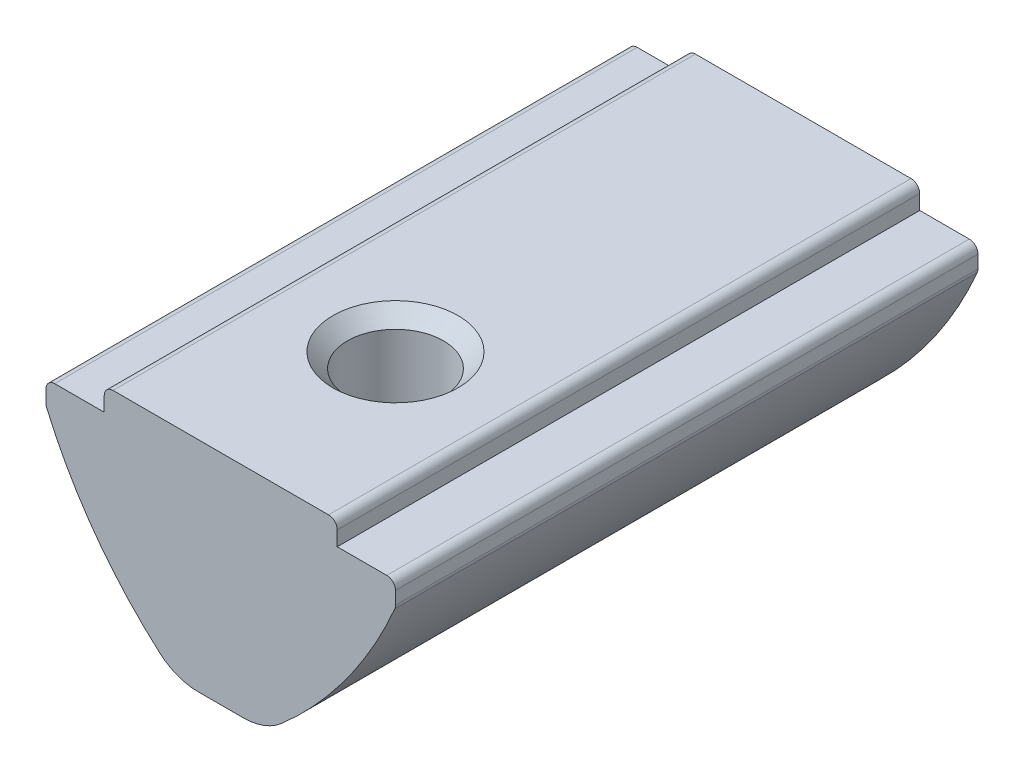
SolidWorks part; units mm, degrees
ref_plane "Спереди" through (0, 0, 0) normal (0, 0, 1) x (1, 0, 0)
ref_plane "Сверху" through (0, 0, 0) normal (0, 1, 0) x (1, 0, 0)
ref_plane "Справа" through (0, 0, 0) normal (1, 0, 0) x (0, 0, -1)
sketch "Эскиз1" plane through (0, 0, 0) normal (0, 0, 1) x (1, 0, 0)
  line L0 (-4, 0) -> (4, 0)
  line L5 (-4, 0) -> (-4, -0.8)
  line L6 (-4, -0.8) -> (-6, -0.8)
  line L7 (-6, -0.8) -> (-6, -1.6)
  line L8 (4, 0) -> (4, -0.8)
  line L9 (4, -0.8) -> (6, -0.8)
  line L10 (6, -0.8) -> (6, -1.6)
  line L11 (-1.5, -7.5) -> (1.5, -7.5)
  arc A0 (-6, -1.6) -> (-1.5, -7.5) centre (7.8062, 4.2641) ccw
  arc A1 (1.5, -7.5) -> (6, -1.6) centre (-7.8062, 4.2641) ccw
  point P0 (0, -7.5)
  point P4 (0, 0)
  dimension "D7" = 15
  dimension "D1" = 8
  dimension "D2" = 12
  dimension "D3" = 0.8
  dimension "D4" = 3
  dimension "D5" = 0.8
  dimension "D6" = 7.5
extrude "Бобышка-Вытянуть1" add sketch "Эскиз1" along normal mid plane 20
fillet "Скругление1" radius 0.3 6 edges at (6, -1.6, 0) (6, -0.8, 0) (-6, -0.8, 0) (-6, -1.6, 0) (4, 0, 0) (-4, 0, 0)
fillet "Скругление2" radius 2 2 edges at (1.5, -7.5, 0) (-1.5, -7.5, 0)
hole_wizard "Отверстие обработанное метчиком M41" positions "Эскиз2" profile "Эскиз4" tap size "M4" standard "ISO" end condition through all
sketch "Эскиз2" plane through (0, 0, 0) normal (0, 1, 0) x (1, 0, 0)
  line L0 (3.7, -10) -> (-3.7, -10) construction
  point P0 (0, -4)
  dimension "D1" = 6
sketch "Эскиз4" plane through (0, 0, 4) normal (1, 0, 0) x (0, 0, 1)
  line L0 (0, 0) -> (0, 7.5)
  line L1 (0, 7.5) -> (1.65, 7.5)
  line L2 (1.65, 7.5) -> (1.65, 0.5)
  line L3 (1.65, 0.5) -> (2.15, 0)
  line L5 (2.15, 0) -> (0, 0)
  line L6 (-1.65, 0.5) -> (-2.15, 0) construction
  line L11 (0, -6.35) -> (0, 107.95) construction
  dimension "Диаметр проходного сверла" = 3.3
  dimension "Глубина проходного сверла" = 7.5
  dimension "Диаметр передней зенковки" = 4.3
  dimension "Угол передней зенковки" = 90
cosmetic thread "Отверстие резьбы1" parameters "D2"=4
sketch "Эскиз5" plane through (0, 0, 0) normal (1, 0, 0) x (0, 0, -1)
  line L1 (6, -4.3) -> (6, -8.3) construction
  line L2 (10, -7.0022) -> (10, -1.657) construction
  line L3 (6, -4.3) -> (6, -8.3)
  line L5 (10, -7.5) -> (-2.5441, -7.5) construction
  arc A0 (6, -4.3) -> (6, -8.3) centre (6, -6.3) ccw
  point P3 (4, -7.4722)
  dimension "D3" = 2
  dimension "D1" = 0.8
  dimension "D2" = 4
revolve "Повернуть1" add sketch "Эскиз5" angle 360 about L1
